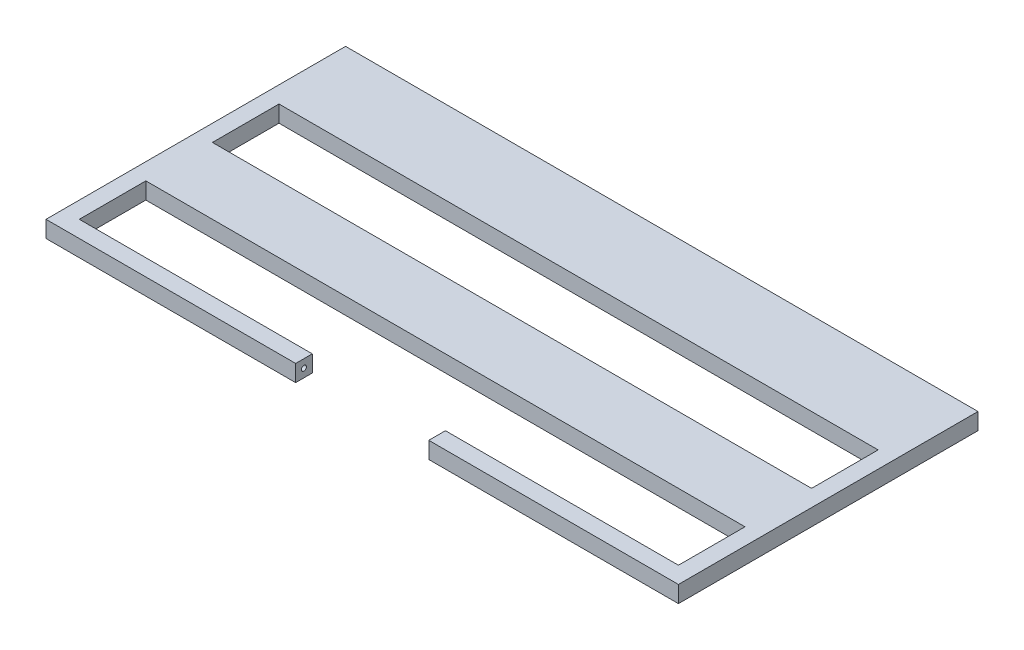
SolidWorks part; units mm, degrees
ref_plane "Alzado" through (0, 0, 0) normal (0, 0, 1) x (1, 0, 0)
ref_plane "Planta" through (0, 0, 0) normal (0, 1, 0) x (1, 0, 0)
ref_plane "Vista lateral" through (0, 0, 0) normal (1, 0, 0) x (0, 0, -1)
sketch "Croquis1" plane through (0, 0, 0) normal (0, 1, 0) x (1, 0, 0)
  line L0 (-450, 425) -> (450, 425)
  line L1 (-475, -600) -> (-100, -600)
  line L2 (-475, -600) -> (-475, 600)
  line L3 (-475, 600) -> (475, 600)
  line L4 (475, -600) -> (475, 600)
  line L5 (-475, -600) -> (475, 600) construction
  line L6 (-475, 600) -> (475, -600) construction
  line L7 (-450, -575) -> (-100, -575)
  line L8 (-450, -575) -> (-450, 575)
  line L9 (-450, 575) -> (450, 575)
  line L10 (450, -575) -> (450, 575)
  line L11 (-450, -575) -> (450, 575) construction
  line L12 (-450, 575) -> (450, -575) construction
  line L13 (-450, 275) -> (450, 275)
  line L14 (-450, 125) -> (450, 125)
  line L15 (-450, -25) -> (450, -25)
  line L16 (-450, -175) -> (450, -175)
  line L17 (-178.125, -225) -> (-176.087, -225)
  line L18 (-450, -375) -> (450, -375)
  line L19 (176.087, -225) -> (178.125, -225)
  line L20 (-450, -475) -> (450, -475)
  line L21 (-450, 575) -> (-450, 425) construction
  line L22 (-100, -600) -> (-100, -575)
  line L23 (100, -600) -> (100, -575)
  line L24 (100, -600) -> (475, -600)
  line L25 (100, -575) -> (450, -575)
  line L26 (-450, -275) -> (450, -275)
  line L27 (-257.2917, -325) -> (-254.3478, -325) [skipped]
  point P0 (0, 0)
  point P6 (0, 0)
  dimension "D1" = 950
  dimension "D2" = 1200
  dimension "D3" = 900
  dimension "D4" = 1150
  dimension "D6" = 150
  dimension "D7" = 375
  dimension "D8" = 200
  dimension "D9" = 100
  dimension "D10" = 100
  dimension "D5" = 8
extrude "Saliente-Extruir2" add sketch "Croquis1" along normal blind 25
sketch "Croquis2" plane through (-100, 0, 0) normal (1, 0, 0) x (0, 0, -1)
  line L0 (-600, 25) -> (-575, 0)
  circle A0 centre (-587.5, 12.5) radius 3.75
  dimension "D1" = 7.5
extrude "Cortar-Extruir1" cut sketch "Croquis2" against normal blind 10 contours L0 A0 | L0 A0
sketch "Croquis3" plane through (0, 0, -600) normal (0, 0, -1) x (-1, 0, 0)
  line L1 (-475, 0) -> (475, 0)
  line L2 (-475, 0) -> (-475, 25)
  line L3 (-475, 25) -> (475, 25)
  line L4 (475, 0) -> (475, 25)
extrude "Cortar-Extruir2" cut sketch "Croquis3" against normal blind 750
